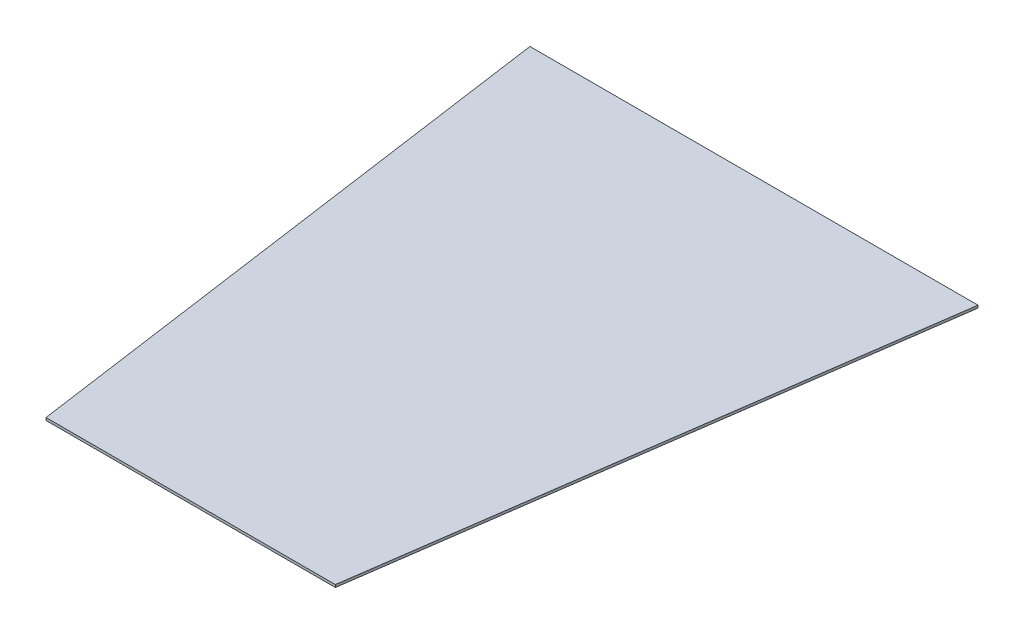
SolidWorks part; units mm, degrees
ref_plane "Front Plane" through (0, 0, 0) normal (0, 0, 1) x (1, 0, 0)
ref_plane "Top Plane" through (0, 0, 0) normal (0, 1, 0) x (1, 0, 0)
ref_plane "Right Plane" through (0, 0, 0) normal (1, 0, 0) x (0, 0, -1)
sketch "Sketch1" plane through (0, 0, 0) normal (0, 1, 0) x (1, 0, 0)
  line L0 (-415.9437, 350) -> (-260.9437, -750)
  line L1 (-415.9437, 350) -> (459.0563, 350)
  line L7 (-260.9437, -750) -> (304.0563, -750)
  line L8 (304.0563, -750) -> (459.0563, 350)
  point P0 (0, 0)
  dimension "D1" = 875
  dimension "D2" = 1100
  dimension "D3" = 565
  dimension "D4" = 155
extrude "Boss-Extrude1" add sketch "Sketch1" along normal blind 5
